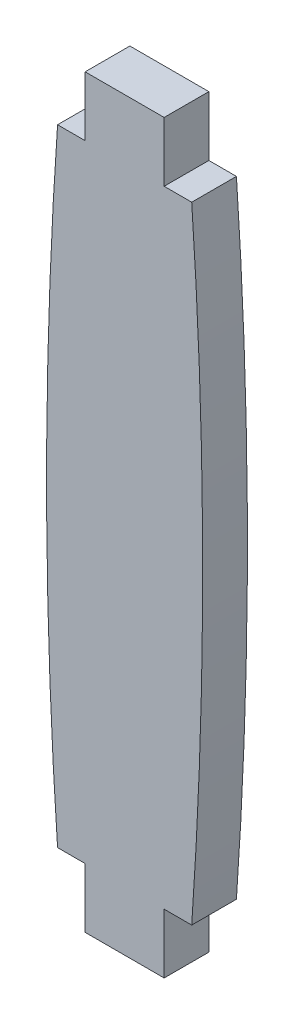
SolidWorks part; units mm, degrees
ref_plane "Alzado" through (0, 0, 0) normal (0, 0, 1) x (1, 0, 0)
ref_plane "Planta" through (0, 0, 0) normal (0, 1, 0) x (1, 0, 0)
ref_plane "Vista lateral" through (0, 0, 0) normal (1, 0, 0) x (0, 0, -1)
sketch "Croquis1" plane through (0, 0, 0) normal (0, 0, 1) x (1, 0, 0)
  line L0 (0, 0) -> (1.85, 0)
  line L1 (1.85, 0) -> (1.85, -4)
  line L2 (1.85, -4) -> (7.15, -4)
  line L3 (7.15, -4) -> (7.15, 0)
  line L4 (7.15, 0) -> (9, 0)
  line L5 (4.5, -4) -> (4.5, 42) construction
  line L6 (0, 42) -> (1.85, 42)
  line L7 (1.85, 42) -> (1.85, 46)
  line L8 (1.85, 46) -> (7.15, 46)
  line L9 (7.15, 46) -> (7.15, 42)
  line L10 (7.15, 42) -> (9, 42)
  arc A0 (0, 0) -> (0, 42) centre (299.2641, 21) cw
  arc A1 (9, 0) -> (9, 42) centre (-290.2641, 21) ccw
  point P17 (0, 0)
  point P19 (0, 0)
  point P20 (4.5, 46)
  dimension "D7" = 300
  dimension "D1" = 4
  dimension "D2" = 4
  dimension "D3" = 5.3
  dimension "D4" = 9
  dimension "D5" = 9
  dimension "D6" = 50
extrude "Saliente-Extruir1" add sketch "Croquis1" along normal blind 3
equation "\"A\"= 3"
equation "\"B\"= 50"
equation "\"C\"= 10mm"
equation "\"D1@Croquis1\"=\"A\"+1"
equation "\"D2@Croquis1\"=\"A\"+1"
equation "\"D3@Croquis1\"=(\"C\"/2)+.3"
equation "\"D6@Croquis1\"=\"B\""
equation "\"D7@Croquis1\"=\"B\"*6"
